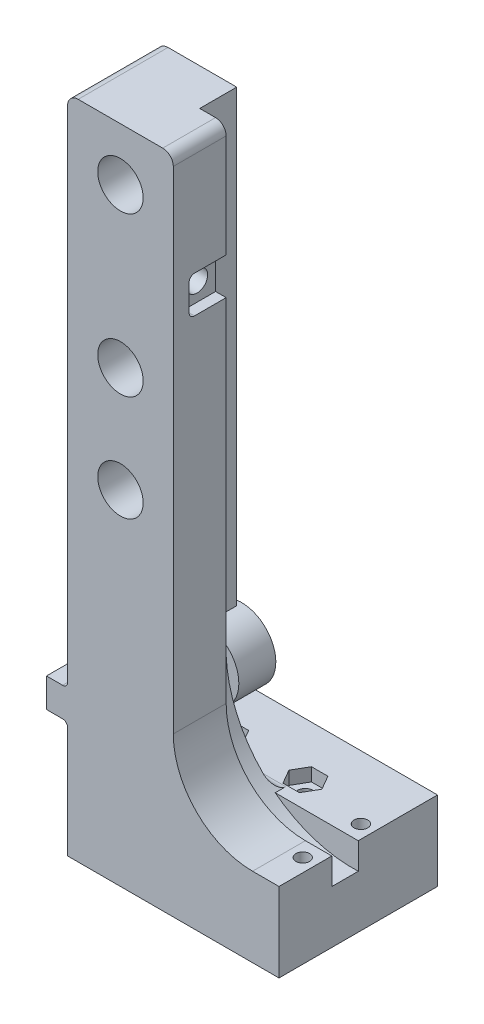
SolidWorks part; units mm, degrees
ref_plane "Front Plane" through (0, 0, 0) normal (0, 0, 1) x (1, 0, 0)
ref_plane "Top Plane" through (0, 0, 0) normal (0, 1, 0) x (1, 0, 0)
ref_plane "Right Plane" through (0, 0, 0) normal (1, 0, 0) x (0, 0, -1)
sketch "Sketch1" plane through (0, 0, 0) normal (0, 0, 1) x (1, 0, 0)
  line L0 (0, 0) -> (0, -125)
  line L1 (0, -125) -> (40, -125)
  line L2 (40, -125) -> (40, -110)
  line L3 (40, -110) -> (20, -110)
  line L4 (20, -110) -> (20, 0)
  line L5 (20, 0) -> (0, 0)
extrude "Boss-Extrude1" add sketch "Sketch1" along normal blind 17
sketch "Sketch3" plane through (0, 0, 0) normal (0, 0, -1) x (-1, 0, 0)
  line L1 (-40, -110) -> (0, -110)
  line L2 (-40, -110) -> (-40, -125)
  line L3 (-40, -125) -> (0, -125)
  line L4 (0, -110) -> (0, -125)
extrude "Boss-Extrude3" add sketch "Sketch3" along normal blind 13
fillet "Fillet1" radius 15 1 edges at (20, -110, 8.5)
sketch "Sketch4" plane through (0, -125, 0) normal (0, -1, 0) x (1, 0, 0)
  circle A0 centre (10, -3) radius 1.5
  circle A1 centre (25, -3) radius 1.5
extrude "Cut-Extrude1" cut sketch "Sketch4" against normal blind 20
sketch "Sketch5" plane through (0, -110, 0) normal (0, 1, 0) x (1, 0, 0)
  line L7 (6.8823, 3) -> (8.4412, 0.3)
  line L14 (8.4412, 0.3) -> (11.5588, 0.3)
  line L15 (11.5588, 0.3) -> (13.1177, 3)
  line L16 (13.1177, 3) -> (11.5588, 5.7)
  line L17 (11.5588, 5.7) -> (8.4412, 5.7)
  line L18 (8.4412, 5.7) -> (6.8823, 3)
  line L19 (21.8823, 3) -> (23.4412, 0.3)
  line L20 (23.4412, 0.3) -> (26.5588, 0.3)
  line L21 (26.5588, 0.3) -> (28.1177, 3)
  line L22 (28.1177, 3) -> (26.5588, 5.7)
  line L23 (26.5588, 5.7) -> (23.4412, 5.7)
  line L24 (23.4412, 5.7) -> (21.8823, 3)
  circle A0 centre (10, 3) radius 2.7 construction
  circle A1 centre (25, 3) radius 2.7 construction
extrude "Cut-Extrude2" cut sketch "Sketch5" against normal blind 2.5
sketch "Sketch6" plane through (0, 0, 17) normal (0, 0, 1) x (1, 0, 0)
  circle A0 centre (10, -10) radius 4.3
  circle A1 centre (10, -40) radius 4.3
  circle A2 centre (10, -60) radius 4.3
extrude "Cut-Extrude3" cut sketch "Sketch6" against normal blind 12
sketch "Sketch7" plane through (0, 0, 5) normal (0, 0, 1) x (1, 0, 0)
  circle A0 centre (10, -10) radius 2.5
  circle A1 centre (10, -40) radius 2.5
  circle A2 centre (10, -60) radius 2.5
extrude "Cut-Extrude4" cut sketch "Sketch7" against normal blind 12
sketch "Sketch8" plane through (0, 0, 0) normal (0, 0, -1) x (-1, 0, 0)
  line L0 (0, -110) -> (0, -85)
  line L1 (0, 0) -> (0, -110) construction
  line L2 (0, -110) -> (-40, -110)
  line L3 (-40, -110) -> (-40, -85)
  line L4 (-40, -85) -> (0, -85)
extrude "Cut-Extrude5" cut sketch "Sketch8" against normal blind 2
sketch "Sketch9" plane through (0, 0, 17) normal (0, 0, 1) x (1, 0, 0)
  line L1 (0, 0) -> (0, -125) construction
  line L3 (0, -103) -> (-4, -103)
  line L4 (0, -103) -> (0, -97.5)
  line L5 (0, -97.5) -> (-4, -97.5)
  line L6 (-4, -103) -> (-4, -97.5)
extrude "Boss-Extrude4" add sketch "Sketch9" against normal blind 23
sketch "Sketch10" plane through (0, 0, -6) normal (0, 0, -1) x (-1, 0, 0)
  line L0 (4, -103) -> (-9.9, -103)
  line L1 (-5.9314, -96) -> (-0.4193, -96)
  line L2 (4, -103) -> (4, -97.5)
  line L5 (-0.4193, -96) -> (-0.4193, -94)
  line L6 (-0.4193, -94) -> (-3.9, -94)
  line L8 (-6.0252, -97.4931) -> (4, -97.5)
  arc A3 (-9.9, -103) -> (-3.9, -94) centre (-9.9, -96.5) cw
  arc A4 (-5.9314, -96) -> (-6.0252, -97.4931) centre (-9.9, -96.5) ccw
extrude "Boss-Extrude5" add sketch "Sketch10" against normal blind 6
sketch "Sketch11" plane through (0.4193, 0, 0) normal (-1, 0, 0) x (0, 0, 1)
  line L1 (-6, -94) -> (0, -94)
  line L2 (-6, -94) -> (-6, -96)
  line L3 (-6, -96) -> (0, -96)
  line L4 (0, -94) -> (0, -96)
extrude "Boss-Extrude6" add sketch "Sketch11" along normal up to surface (4.4193 mm away) up to face at (-4, -99.7, 4.4)
sketch "Sketch12" plane through (0, -94, 0) normal (0, 1, 0) x (1, 0, 0)
  circle A0 centre (-0.05, 3) radius 1.25
extrude "Cut-Extrude7" cut sketch "Sketch12" against normal blind 10
fillet "Fillet4" radius 0.95 2 edges at (0, -97.5, 9.5) (0, -103, 9.5)
fillet "Fillet6" radius 2 2 edges at (20, 0, 8.5) (0, 0, 8.5)
sketch "Sketch13" plane through (0, 0, 0) normal (0, 0, 1) x (1, 0, 0)
  circle A1 centre (9.9, -96.5) radius 2.15
  circle A3 centre (9.9, -96.5) radius 6.5
extrude "Boss-Extrude7" add sketch "Sketch13" along normal blind 1
sketch "Sketch14" plane through (0, 0, -6) normal (0, 0, -1) x (-1, 0, 0)
  line L1 (4, -96) -> (-9.2497, -96)
  line L2 (4, -96) -> (4, -97.5)
  line L3 (4, -97.5) -> (-9.2497, -97.5)
  line L4 (-9.2497, -96) -> (-9.2497, -97.5)
extrude "Cut-Extrude8" cut sketch "Sketch14" against normal up to surface (7 mm away) up to face at (16.4, -96.5, 1)
sketch "Sketch15" plane through (0, 0, 0) normal (0, 0, 1) x (1, 0, 0)
  line L7 (9.9, -103) -> (0, -103) construction
  line L8 (0, -97.5) -> (2.5, -97.5)
  line L9 (0, -97.5) -> (0, -103)
  line L10 (0, -103) -> (2.5, -103)
  line L11 (2.5, -97.5) -> (2.5, -103)
extrude "Boss-Extrude8" add sketch "Sketch15" along normal blind 10
sketch "Sketch16" plane through (0, 0, -6) normal (0, 0, -1) x (-1, 0, 0)
  circle A0 centre (-9.9, -96.5) radius 4.1
extrude "Cut-Extrude9" cut sketch "Sketch16" against normal up to surface (6 mm away) up to face at (9.9518, -96.4946, 0)
sketch "Sketch17" plane through (20, 0, 0) normal (1, 0, 0) x (0, 0, -1)
  line L1 (0, 0) -> (-7, 0)
  line L2 (0, 0) -> (0, -89.7591)
  line L3 (0, -89.7591) -> (-7, -89.7591)
  line L4 (-7, 0) -> (-7, -89.7591)
extrude "Cut-Extrude10" cut sketch "Sketch17" against normal blind 5
sketch "Sketch18" plane through (0, 0, 2) normal (0, 0, -1) x (-1, 0, 0)
  circle A0 centre (-39, -91) radius 24.0321
extrude "Cut-Extrude11" cut sketch "Sketch18" against normal blind 5
sketch "Sketch20" plane through (0, -110, 0) normal (0, 1, 0) x (1, 0, 0)
  circle A0 centre (37.5, -10) radius 1.3
  circle A1 centre (37.5, 1) radius 1.3
extrude "Cut-Extrude12" cut sketch "Sketch20" against normal blind 10
fillet "Fillet7" radius 0.5 2 edges at (2.5, -100.25, 0) (2.5, -100.25, 2)
fillet "Fillet8" radius 2 1 edges at (12.1424, -110, 2)
fillet "Fillet9" radius 2 1 edges at (3.9, -94, -3)
fillet "Fillet10" radius 1 1 edges at (1.025, -103, 2)
fillet "Fillet11" radius 1 1 edges at (1.025, -97.5, 2)
sketch "Sketch23" plane through (20, 0, 0) normal (1, 0, 0) x (0, 0, -1)
  line L0 (-7, -21.5) -> (-7, -28.5)
  line L2 (-7, -2) -> (-7, -95) construction
  line L3 (-7, -21.5) -> (-13, -21.5)
  line L4 (-14, -22.5) -> (-14, -27.5)
  line L5 (-13, -28.5) -> (-7, -28.5)
  line L6 (-7, 0) -> (-7, -89.7591) construction
  arc A0 (-14, -27.5) -> (-13, -28.5) centre (-13, -27.5) ccw
  arc A1 (-13, -21.5) -> (-14, -22.5) centre (-13, -22.5) ccw
  dimension "D1" = 1
extrude "Cut-Extrude15" cut sketch "Sketch23" against normal blind 2
sketch "Sketch24" plane through (18, 0, 0) normal (1, 0, 0) x (0, 0, -1)
  circle A0 centre (-10.5, -25) radius 2
extrude "Cut-Extrude16" cut sketch "Sketch24" against normal blind 5
